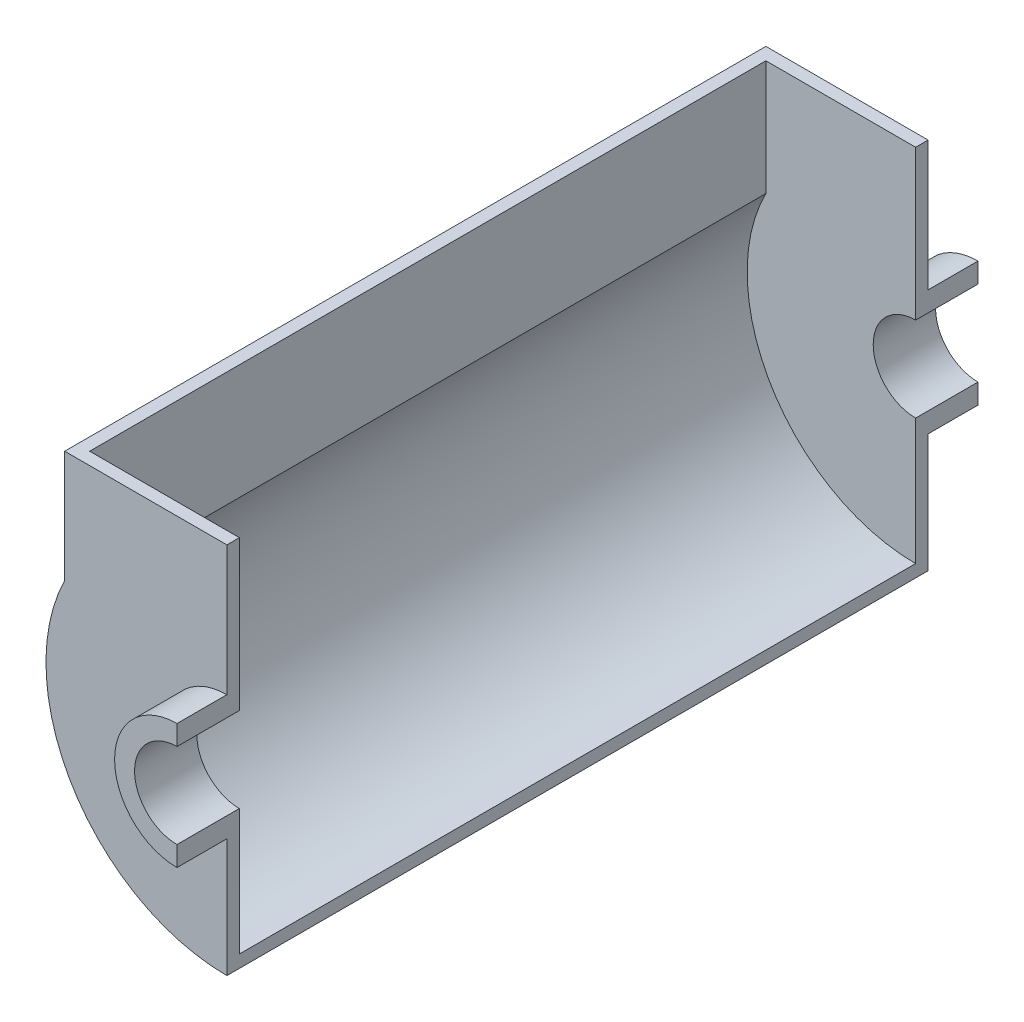
SolidWorks part; units mm, degrees
ref_plane "Front Plane" through (0, 0, 0) normal (0, 0, 1) x (1, 0, 0)
ref_plane "Top Plane" through (0, 0, 0) normal (0, 1, 0) x (1, 0, 0)
ref_plane "Right Plane" through (0, 0, 0) normal (1, 0, 0) x (0, 0, -1)
sketch "Sketch1" plane through (0, 0, 0) normal (0, 0, 1) x (1, 0, 0)
  line L0 (0, 635) -> (0, 431.8)
  line L1 (0, -431.8) -> (0, -635)
  arc A0 (0, 635) -> (0, -635) centre (0, 0) ccw
  arc A1 (0, 431.8) -> (0, -431.8) centre (0, 0) ccw
  dimension "D1" = 1270
  dimension "D2" = 863.6
extrude "Boss-Extrude1" add sketch "Sketch1" along normal blind 508 and the other way blind 127
sketch "Sketch2" plane through (0, 0, 0) normal (0, 0, 1) x (1, 0, 0)
  line L0 (0, 635) -> (0, 1955.8)
  line L1 (0, 1955.8) -> (-1651, 1955.8)
  line L2 (-1651, 1955.8) -> (-1651, 815.6723)
  line L3 (0, -635) -> (0, -1841.5)
  arc A0 (0, 635) -> (0, -635) centre (0, 0) ccw construction
  arc A1 (0, 635) -> (0, -635) centre (0, 0) ccw
  arc A2 (-1651, 815.6723) -> (0, -1841.5) centre (0, 0) ccw
  dimension "D3" = 1841.5
  dimension "D1" = 1320.8
  dimension "D2" = 1651
extrude "Boss-Extrude2" add sketch "Sketch2" against normal blind 127
ref_plane "Plane1" through (0, 0, -3568.7) normal (0, 0, 1) x (1, 0, 0)
mirror "Mirror1" about plane through (0, 0, -3568.7) normal (0, 0, 1) of bodies 102
sketch "Sketch3" plane through (0, 0, -127) normal (0, 0, -1) x (-1, 0, 0)
  line L0 (1651, 1955.8) -> (1651, 815.6723) construction
  line L1 (1651, 1955.8) -> (1651, 815.6723)
  line L2 (1524, 1955.8) -> (1524, 785.4516)
  line L3 (1651, 1955.8) -> (1524, 1955.8)
  line L4 (0, -1841.5) -> (0, -1714.5)
  arc A0 (0, -1841.5) -> (1651, 815.6723) centre (0, 0) ccw construction
  arc A1 (0, -1841.5) -> (1651, 815.6723) centre (0, 0) ccw
  arc A2 (0, -1714.5) -> (1524, 785.4516) centre (0, 0) ccw
  dimension "D1" = 127
extrude "Boss-Extrude3" add sketch "Sketch3" along normal up to surface (6883.4 mm away)
